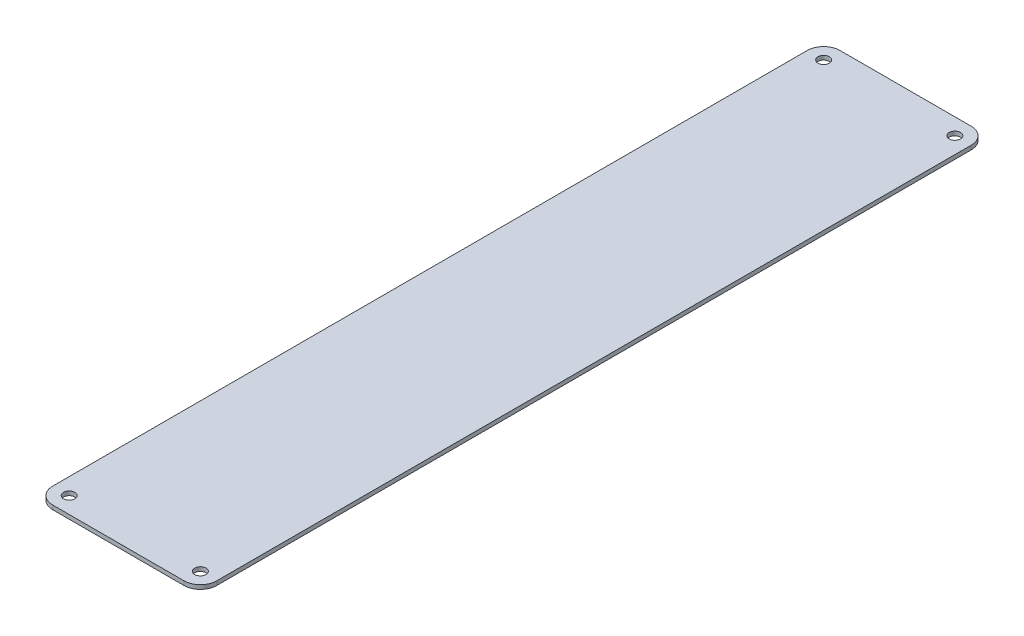
SolidWorks part; units mm, degrees
ref_plane "Front Plane" through (0, 0, 0) normal (0, 0, 1) x (1, 0, 0)
ref_plane "Top Plane" through (0, 0, 0) normal (0, 1, 0) x (1, 0, 0)
ref_plane "Right Plane" through (0, 0, 0) normal (1, 0, 0) x (0, 0, -1)
sketch "Sketch1" plane through (0, 0, 0) normal (0, 1, 0) x (1, 0, 0)
  line L1 (6.35, 0) -> (57.15, 0)
  line L2 (0, 6.35) -> (0, 298.45)
  line L3 (6.35, 304.8) -> (57.15, 304.8)
  line L4 (63.5, 6.35) -> (63.5, 298.45)
  circle A0 centre (57.15, 298.45) radius 2.1828
  circle A1 centre (6.35, 298.45) radius 2.1828
  circle A2 centre (6.35, 6.35) radius 2.1828
  circle A3 centre (57.15, 6.35) radius 2.1828
  arc A4 (6.35, 304.8) -> (0, 298.45) centre (6.35, 298.45) ccw
  arc A5 (6.35, 0) -> (0, 6.35) centre (6.35, 6.35) cw
  arc A6 (63.5, 6.35) -> (57.15, 0) centre (57.15, 6.35) cw
  arc A7 (63.5, 298.45) -> (57.15, 304.8) centre (57.15, 298.45) ccw
  point P16 (0, 304.8)
  point P19 (0, 0)
  point P22 (63.5, 0)
  dimension "D6" = 4.3656
  dimension "D8" = 4.3656
  dimension "D9" = 6.35
  dimension "D10" = 6.35
  dimension "D11" = 6.35
  dimension "D14" = 4.3656
  dimension "D17" = 4.3656
  dimension "D18" = 6.35
  dimension "D1" = 63.5
  dimension "D2" = 304.8
  dimension "D3" = 6.35
  dimension "D4" = 6.35
  dimension "D5" = 6.35
  dimension "D7" = 6.35
  dimension "D12" = 6.35
  dimension "D13" = 6.35
  dimension "D15" = 6.35
  dimension "D16" = 6.35
extrude "Boss-Extrude1" add sketch "Sketch1" along normal mid plane 1.5875
